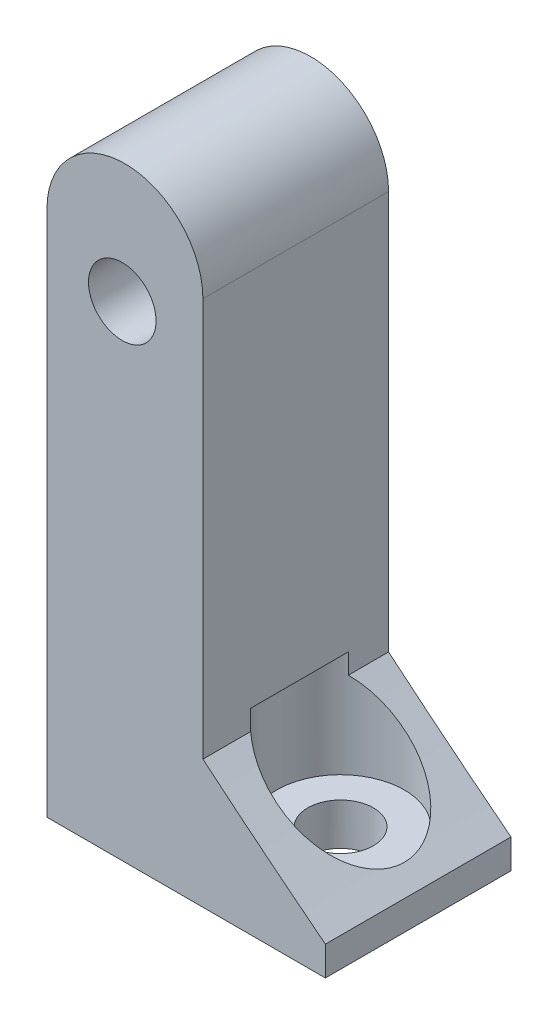
SolidWorks part; units mm, degrees
ref_plane "Front Plane" through (0, 0, 0) normal (0, 0, 1) x (1, 0, 0)
ref_plane "Top Plane" through (0, 0, 0) normal (0, 1, 0) x (1, 0, 0)
ref_plane "Right Plane" through (0, 0, 0) normal (1, 0, 0) x (0, 0, -1)
sketch "Sketch1" plane through (0, 0, 287.675) normal (0, 0, -1) x (-1, 0, 0)
  line L0 (-152.2518, 257.1792) -> (-150.2586, 257.1792)
  line L2 (-150.2586, 278.6168) -> (-150.2586, 257.1792)
  line L5 (-152.2518, 257.1792) -> (-152.2518, 278.2866)
  line L6 (-156.6086, 278.2866) -> (-150.2586, 278.2866) construction
  line L8 (-129.232, 277.112) -> (-129.232, 316.6536)
  line L9 (-139.9, 289.375) -> (-139.9, 316.6536)
  line L10 (-148.2774, 280.598) -> (-148.2774, 288.218) construction
  line L11 (-129.232, 277.112) -> (-149.0902, 277.112)
  line L12 (-149.0902, 276.9734) -> (-149.0902, 278.6168) construction
  line L13 (-149.0902, 277.112) -> (-149.0902, 278.6168)
  line L14 (-148.2774, 279.4296) -> (-136.3902, 279.4296)
  line L15 (-136.3902, 279.4296) -> (-136.3902, 280.598)
  line L16 (-136.3902, 280.598) -> (-148.2774, 280.598)
  arc A0 (-148.2774, 280.598) -> (-150.2586, 278.6168) centre (-148.2774, 278.6168) ccw
  arc A1 (-139.9, 316.6536) -> (-129.232, 316.6536) centre (-134.566, 316.6536) cw
  arc A2 (-152.2518, 278.2866) -> (-148.2774, 282.6048) centre (-148.2774, 278.6168) cw
  arc A3 (-139.9, 289.375) -> (-148.2774, 282.6048) centre (-324.7827, 509.5799) cw
  circle A4 centre (-134.3836, 313.7275) radius 2.3114
  arc A5 (-149.0902, 278.6168) -> (-148.2774, 279.4296) centre (-148.2774, 278.6168) cw
  dimension "D3" = 5.334
  dimension "D4" = 4.6228
  dimension "D2" = 10.668
extrude "Boss-Extrude1" add sketch "Sketch1" along normal blind 12.7
sketch "Sketch2" plane through (150.2586, 0, 0) normal (-1, 0, 0) x (0, 0, 1)
  circle A0 centre (281.2302, 274.3127) radius 2.3114
  circle A1 centre (281.2302, 261.6127) radius 2.3114
  dimension "D1" = 4.6228
  dimension "D2" = 4.6228
  dimension "D3" = 12.7
extrude "Cut-Extrude1" cut sketch "Sketch2" against normal blind 12.7
ref_plane "Plane1" through (0, 290.758, 0) normal (0, 1, 0) x (1, 0, 0)
sketch "Sketch3" plane through (0, 290.758, 0) normal (0, 1, 0) x (1, 0, 0)
  point P5 (142.708, -281.0674)
hole_wizard "CBORE for #8 Button Head Cap Screw1" positions "Sketch4" profile "Sketch5" counterbore size "#8" standard "ANSI Inch"
sketch "Sketch4" plane through (0, 290.758, 0) normal (0, 1, 0) x (1, 0, 0)
  point P0 (142.708, -281.0674)
sketch "Sketch5" plane through (142.708, 290.758, 281.0674) normal (1, 0, 0) x (0, 0, 1)
  line L0 (0, 0) -> (0, 33.5788)
  line L1 (0, 33.5788) -> (2.2479, 33.5788)
  line L3 (2.2479, 33.5788) -> (2.2479, 7.2898)
  line L4 (2.2479, 7.2898) -> (4.3663, 7.2898)
  line L5 (4.3663, 7.2898) -> (4.3663, 0)
  line L7 (4.3663, 0) -> (0, 0)
  line L11 (0, -6.35) -> (0, 107.95) construction
  dimension "Thru Hole Dia." = 4.4958
  dimension "Thru Hole Depth" = 33.5788
  dimension "C'Bore Dia." = 8.7325
  dimension "C'Bore Depth" = 7.2898
sketch "Sketch6" plane through (0, 0, 274.975) normal (0, 0, -1) x (-1, 0, 0)
  line L1 (-148.2774, 282.6048) -> (-162.3989, 282.6048)
  line L2 (-148.2774, 282.6048) -> (-148.2774, 252.7709)
  line L3 (-148.2774, 252.7709) -> (-162.3989, 252.7709)
  line L4 (-162.3989, 282.6048) -> (-162.3989, 252.7709)
extrude "Cut-Extrude2" cut sketch "Sketch6" against normal blind 12.7
sketch "Sketch7" plane through (0, 0, 274.975) normal (0, 0, -1) x (-1, 0, 0)
  line L1 (-148.2774, 280.598) -> (-119.5896, 280.598)
  line L2 (-148.2774, 280.598) -> (-148.2774, 264.9296)
  line L3 (-148.2774, 264.9296) -> (-119.5896, 264.9296)
  line L4 (-119.5896, 280.598) -> (-119.5896, 264.9296)
extrude "Cut-Extrude3" cut sketch "Sketch7" against normal blind 12.7
